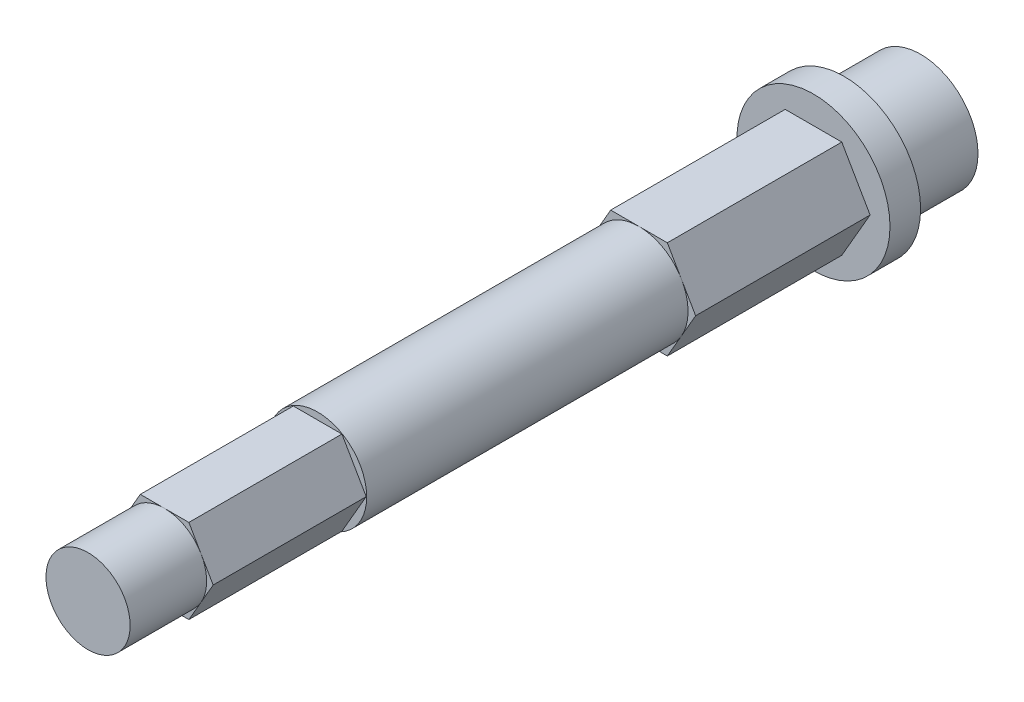
SolidWorks part; units mm, degrees
ref_plane "Front Plane" through (0, 0, 0) normal (0, 0, 1) x (1, 0, 0)
ref_plane "Top Plane" through (0, 0, 0) normal (0, 1, 0) x (1, 0, 0)
ref_plane "Right Plane" through (0, 0, 0) normal (1, 0, 0) x (0, 0, -1)
sketch "Sketch1" plane through (0, 0, 0) normal (0, 0, 1) x (1, 0, 0)
  circle A0 centre (0, 0) radius 3.75
  dimension "D1" = 7.5
extrude "Boss-Extrude1" add sketch "Sketch1" along normal blind 5
sketch "Sketch2" plane through (0, 0, 5) normal (0, 0, 1) x (1, 0, 0)
  circle A0 centre (0, 0) radius 5
  dimension "D1" = 10
extrude "Boss-Extrude2" add sketch "Sketch2" along normal blind 2
sketch "Sketch3" plane through (0, 0, 7) normal (0, 0, 1) x (1, 0, 0)
  line L7 (3.7, 0) -> (1.85, 3.2043)
  line L8 (1.85, 3.2043) -> (-1.85, 3.2043)
  line L9 (-1.85, 3.2043) -> (-3.7, 0)
  line L10 (-3.7, 0) -> (-1.85, -3.2043)
  line L11 (-1.85, -3.2043) -> (1.85, -3.2043)
  line L12 (1.85, -3.2043) -> (3.7, 0)
  circle A0 centre (0, 0) radius 3.7 construction
  circle A1 centre (0, 0) radius 3.2043 construction
  dimension "D1" = 7.4
extrude "Boss-Extrude3" add sketch "Sketch3" along normal blind 11.4
sketch "Sketch4" plane through (0, 0, 18.4) normal (0, 0, 1) x (1, 0, 0)
  line L2 (-1.85, 3.2043) -> (-3.7, 0) construction
  circle A0 centre (0, 0) radius 3.2043
extrude "Boss-Extrude4" add sketch "Sketch4" along normal blind 21
sketch "Sketch5" plane through (0, 0, 39.4) normal (0, 0, 1) x (1, 0, 0)
  line L1 (3.175, 0) -> (1.5875, 2.7496)
  line L2 (1.5875, 2.7496) -> (-1.5875, 2.7496)
  line L3 (-1.5875, 2.7496) -> (-3.175, 0)
  line L4 (-3.175, 0) -> (-1.5875, -2.7496)
  line L5 (-1.5875, -2.7496) -> (1.5875, -2.7496)
  line L6 (1.5875, -2.7496) -> (3.175, 0)
  circle A0 centre (0, 0) radius 2.7496 construction
  circle A1 centre (0, 0) radius 3.175 construction
  point P1 (3.0406, 0)
  point P11 (3.15, 0)
  dimension "D1" = 6.35
extrude "Boss-Extrude5" add sketch "Sketch5" along normal blind 10
sketch "Sketch6" plane through (0, 0, 49.4) normal (0, 0, 1) x (1, 0, 0)
  line L0 (1.5875, 2.7496) -> (-1.5875, 2.7496) construction
  circle A0 centre (0, 0) radius 2.7496
extrude "Boss-Extrude6" add sketch "Sketch6" along normal blind 5
